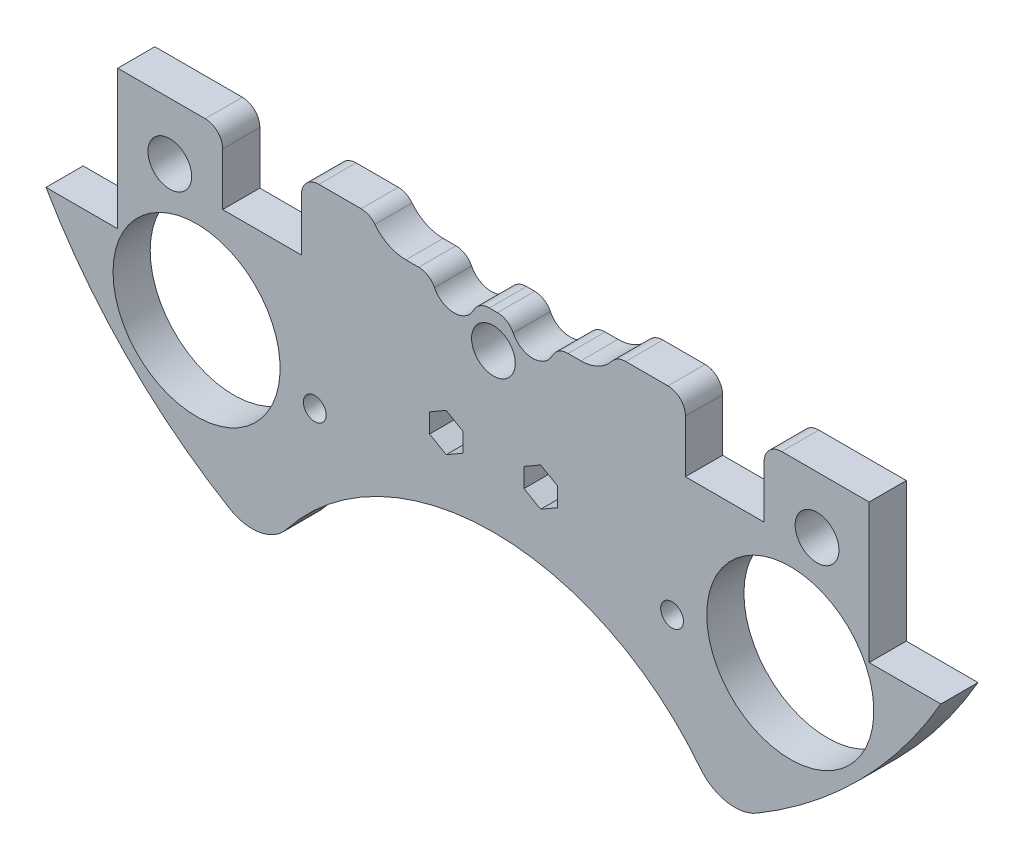
SolidWorks part; units mm, degrees
ref_plane "Front Plane" through (0, 0, 0) normal (0, 0, 1) x (1, 0, 0)
ref_plane "Top Plane" through (0, 0, 0) normal (0, 1, 0) x (1, 0, 0)
ref_plane "Right Plane" through (0, 0, 0) normal (1, 0, 0) x (0, 0, -1)
sketch "Sketch1" plane through (0, 0, 0) normal (0, 0, 1) x (1, 0, 0)
  line L0 (0, 0) -> (-82.1241, 0) construction
  line L1 (0, 0) -> (0, 95.6219) construction
  line L3 (-64.9644, 37.338) -> (-54.5504, 37.338)
  line L5 (-64.9644, -37.338) -> (-54.5504, -37.338)
  line L6 (-54.5504, 37.338) -> (-54.5504, -37.338)
  line L7 (64.9644, -37.338) -> (54.5504, -37.338)
  line L8 (64.9644, 37.338) -> (54.5504, 37.338)
  line L9 (54.5504, 37.338) -> (54.5504, -37.338)
  arc A0 (-64.9644, -37.338) -> (64.9644, -37.338) centre (0, 0) ccw
  circle A1 centre (-46.482, 11.049) radius 1.651
  circle A2 centre (-21.0833, 10.795) radius 1.651
  circle A3 centre (-21.0833, -10.795) radius 1.651
  circle A4 centre (-46.482, -11.049) radius 1.651
  circle A5 centre (46.482, -11.049) radius 1.651
  circle A6 centre (21.0833, -10.795) radius 1.651
  circle A7 centre (21.0833, 10.795) radius 1.651
  circle A8 centre (46.482, 11.049) radius 1.651
  arc A9 (64.9644, 37.338) -> (-64.9644, 37.338) centre (0, 0) ccw
  dimension "D2" = 3.302
  dimension "D3" = 3.302
  dimension "D4" = 25.4
  dimension "D5" = 10.795
  dimension "D10" = 46.482
  dimension "D6" = 74.676
  dimension "D7" = 10.414
  dimension "D8" = 74.93
  dimension "D9" = 74.93
  dimension "D11" = 37.338
extrude "Boss-Extrude2" add sketch "Sketch1" along normal blind 5.3975
sketch "Sketch2" plane through (0, 0, 5.3975) normal (0, 0, 1) x (1, 0, 0)
  line L0 (0, 68.58) -> (0, 55.88) construction
  line L1 (-9.525, 68.58) -> (9.525, 68.58)
  line L2 (-9.525, 68.58) -> (-9.525, 55.88)
  line L3 (-9.525, 55.88) -> (9.525, 55.88)
  line L4 (9.525, 68.58) -> (9.525, 55.88)
  line L5 (-9.525, 62.23) -> (9.525, 62.23) construction
  arc A0 (64.9644, 37.338) -> (-64.9644, 37.338) centre (0, 0) ccw construction
  circle A1 centre (-21.0833, 10.795) radius 1.651 construction
  circle A2 centre (21.0833, 10.795) radius 1.651 construction
  circle A3 centre (-6.731, 62.23) radius 1.143
  circle A4 centre (6.731, 62.23) radius 1.143
  dimension "D4" = 2.286
  dimension "D5" = 0
  dimension "D6" = 6.731
  dimension "D1" = 19.05
  dimension "D2" = 12.7
  dimension "D3" = 55.88
extrude "Cut-Extrude1" cut sketch "Sketch2" against normal through all contours A3 | A4
sketch "Sketch3" plane through (0, 0, 0) normal (0, 0, -1) x (-1, 0, 0)
  line L0 (0, 0) -> (0, -116.2908) construction
  line L1 (0, 0) -> (-153.8039, 0) construction
  line L2 (0, 0) -> (15.2681, -56.9814) construction
  circle A4 centre (-43.1052, -43.1052) radius 12.1285
  circle A6 centre (14.224, -34.29) radius 12.1285
  circle A7 centre (14.224, 34.29) radius 12.1285
  circle A8 centre (-43.1052, 43.1052) radius 12.1285
  circle A11 centre (43.1052, 43.1052) radius 12.1285
  circle A12 centre (-14.224, 34.29) radius 12.1285
  circle A13 centre (-14.224, -34.29) radius 12.1285
  circle A14 centre (43.1052, -43.1052) radius 12.1285
  point P36 (0, 0)
  point P53 (0, 0)
  point P55 (0, 0)
  dimension "D1" = 14.224
  dimension "D2" = 34.29
  dimension "D4" = 15
  dimension "D8" = 24.257
extrude "Cut-Extrude2" cut sketch "Sketch3" against normal through all
sketch "Sketch4" plane through (0, 0, 0) normal (0, 0, -1) x (-1, 0, 0)
  line L1 (-15.7702, 56.3138) -> (12.7925, 56.3138)
  line L2 (-15.7702, 56.3138) -> (-15.7702, 67.9913)
  line L3 (-15.7702, 67.9913) -> (12.7925, 67.9913)
  line L4 (12.7925, 56.3138) -> (12.7925, 67.9913)
extrude "Boss-Extrude3" add sketch "Sketch4" against normal up to surface (5.3975 mm away) up to face at (-55.2337, -43.1052, 5.3975)
sketch "Sketch5" plane through (0, 0, 0) normal (0, 0, -1) x (-1, 0, 0)
  line L1 (-85.044, -17.145) -> (131.6774, -17.145)
  line L2 (-85.044, -17.145) -> (-85.044, 113.4242)
  line L3 (-85.044, 113.4242) -> (131.6774, 113.4242)
  line L4 (131.6774, -17.145) -> (131.6774, 113.4242)
  circle A0 centre (-21.0833, -10.795) radius 1.651 construction
  dimension "D1" = 6.35
extrude "Cut-Extrude4" cut sketch "Sketch5" against normal through all contours L2 L3 L4 L1
sketch "Sketch6" plane through (0, 0, 0) normal (0, 0, -1) x (-1, 0, 0)
  line L0 (-33.02, -67.2621) -> (33.02, -67.2621)
  line L1 (0, 0) -> (0, -146.3858) construction
  arc A0 (-64.9644, -37.338) -> (64.9644, -37.338) centre (0, 0) ccw construction
  circle A1 centre (0, -86.3121) radius 38.1
  dimension "D2" = 76.2
  dimension "D1" = 66.04
  dimension "D3" = 19.05
extrude "Cut-Extrude5" cut sketch "Sketch6" against normal blind 60.96 contours A1
extrude "Cut-Extrude6" cut sketch "Sketch7" against normal through all both and the other way through all
sketch "Sketch7" plane through (-31.3134, 132.614, 31.75) normal (0, 0, 1) x (0, 1, 0)
  line L0 (-132.614, -31.3134) -> (-132.614, 57.8454) construction
  line L1 (-132.614, -31.3134) -> (-222.516, -31.3134) construction
  circle A0 centre (-158.014, 14.4066) radius 3.175
  circle A1 centre (-173.254, -31.3134) radius 3.175
  circle A3 centre (-158.014, -77.0334) radius 3.175
  circle A4 centre (-107.214, -77.0334) radius 3.175
  circle A5 centre (-91.974, -31.3134) radius 3.175
  circle A6 centre (-107.214, 14.4066) radius 3.175
fillet "Fillet1" radius 6.35 1 edges at (-33.001, -67.2714, 2.6987)
fillet "Fillet2" radius 6.35 1 edges at (33.001, -67.2714, 2.6987)
extrude "Cut-Extrude8" cut sketch "Sketch9" against normal blind 29.21
sketch "Sketch9" plane through (-31.3134, 132.559, 28.575) normal (0, 0, 1) x (0, 1, 0)
  line L0 (-132.559, -31.3134) -> (6.1626, -31.3134) construction
  line L2 (-132.559, -31.3134) -> (-132.559, -122.6589) construction
  circle A0 centre (-190.979, 2.9766) radius 1.651
  circle A2 centre (-154.784, -31.3134) radius 1.651
  circle A3 centre (-190.979, -65.6034) radius 1.651
  circle A4 centre (-110.334, -31.3134) radius 1.651
  circle A5 centre (-74.139, -65.6034) radius 1.651
  circle A6 centre (-74.139, 2.9766) radius 1.651
extrude "Cut-Extrude99" cut sketch "Sketch100" against normal blind 29.21
sketch "Sketch100" plane through (-31.3134, 132.559, 22.225) normal (0, 0, 1) x (0, 1, 0)
  line L0 (-143.7712, -34.3645) -> (6.1626, -34.3645) construction
  line L2 (-143.7712, -34.3645) -> (-143.7712, -122.6589) construction
  circle A0 centre (-202.1912, -0.0745) radius 1.651
  circle A2 centre (-165.9962, -34.3645) radius 1.651
  circle A3 centre (-202.1912, -68.6545) radius 1.651
  circle A4 centre (-121.5462, -34.3645) radius 1.651
  circle A5 centre (-85.3512, -68.6545) radius 1.651
  circle A6 centre (-85.3512, -0.0745) radius 1.651
sketch "Sketch102" plane through (0, 0, 0) normal (0, 0, -1) x (-1, 0, 0)
  line L0 (-54.5504, -17.145) -> (54.5504, -17.145) construction
  line L1 (-39.3104, -17.145) -> (-27.8804, -17.145)
  line L2 (-39.3104, -17.145) -> (-39.3104, -27.305)
  line L3 (-39.3104, -27.305) -> (-27.8804, -27.305)
  line L4 (-27.8804, -17.145) -> (-27.8804, -27.305)
  line L5 (0, 15.7454) -> (0, -80.7771) construction
  line L6 (27.8804, -17.145) -> (39.3104, -17.145)
  line L7 (27.8804, -17.145) -> (27.8804, -27.305)
  line L8 (27.8804, -27.305) -> (39.3104, -27.305)
  line L9 (39.3104, -17.145) -> (39.3104, -27.305)
  line L10 (-54.5504, -37.338) -> (-54.5504, -17.145) construction
  dimension "D1" = 11.43
  dimension "D2" = 10.16
  dimension "D3" = 15.24
extrude "Cut-Extrude101" cut sketch "Sketch102" against normal through all
extrude "Cut-Extrude157" cut sketch "Sketch158" against normal blind 97.79
sketch "Sketch158" plane through (30.092, 4.0835, -24.638) normal (0, 0, -1) x (-1, 0, 0)
  line L0 (30.092, -29.4835) -> (30.092, 6.2385) construction
  circle A0 centre (4.1544, -49.7288) radius 1.651
  circle A4 centre (56.0296, -49.7288) radius 1.651
  circle A5 centre (4.1544, 41.3825) radius 1.651
  circle A9 centre (56.0296, 41.3825) radius 1.651
extrude "Cut-Extrude211" cut sketch "Sketch212" against normal blind 48.768 and the other way blind 103.378
sketch "Sketch212" plane through (30.092, 4.0835, 11.4935) normal (0, 0, -1) x (-1, 0, 0)
  line L0 (30.092, -4.0835) -> (148.6336, -4.0835) construction
  line L1 (30.092, -4.0835) -> (30.092, 90.452) construction
  circle A0 centre (-16.898, 21.3165) radius 3.175
  circle A1 centre (77.082, 21.3165) radius 3.175
  circle A2 centre (30.092, 21.3165) radius 3.175
  circle A4 centre (77.082, -29.4835) radius 3.175
  circle A5 centre (30.092, -29.4835) radius 3.175
  circle A6 centre (-16.898, -29.4835) radius 3.175
sketch "Sketch105" plane through (0, 0, 0) normal (0, 0, -1) x (-1, 0, 0)
  line L0 (0, 0) -> (0, -8.89) construction
  line L1 (-12.7, -20.32) -> (-8.89, -20.32)
  line L2 (-12.7, -8.89) -> (12.7, -8.89)
  line L3 (0, -20.32) -> (0, -99.3188) construction
  line L4 (8.89, -20.32) -> (12.7, -20.32)
  line L5 (-2.54, -20.32) -> (2.54, -20.32)
  arc A0 (-12.7, -8.89) -> (-12.7, -20.32) centre (-12.7, -14.605) ccw
  arc A1 (12.7, -8.89) -> (12.7, -20.32) centre (12.7, -14.605) cw
  arc A2 (-8.89, -20.32) -> (-2.54, -20.32) centre (-5.715, -20.32) ccw
  arc A3 (2.54, -20.32) -> (8.89, -20.32) centre (5.715, -20.32) ccw
  dimension "D1" = 11.43
  dimension "D4" = 6.35
  dimension "D5" = 6.35
  dimension "D2" = 12.7
  dimension "D3" = 14.605
  dimension "D6" = 11.43
  dimension "D7" = 5.715
  dimension "D8" = 20.32
extrude "Cut-Extrude104" cut sketch "Sketch105" against normal blind 10
fillet "Fillet3" radius 2.54 10 edges at (-39.3104, -17.145, 2.6987) (-27.8804, -17.145, 2.6987) (-17.8195, -17.145, 2.6987) (-8.89, -20.32, 2.6987) (-2.54, -20.32, 2.6987) (2.54, -20.32, 2.6987) (8.89, -20.32, 2.6987) (17.8195, -17.145, 2.6987) (27.8804, -17.145, 2.6987) (39.3104, -17.145, 2.6987)
sketch "Sketch225" plane through (0, 0, 0) normal (0, 0, -1) x (-1, 0, 0)
  circle A0 centre (-14.224, -34.29) radius 12.1285
  circle A1 centre (14.224, -34.29) radius 12.1285
  circle A2 centre (-14.224, -34.29) radius 12.1285 construction
  circle A3 centre (14.224, -34.29) radius 12.1285 construction
extrude "Boss-Extrude4" add sketch "Sketch225" against normal up to surface (5.3975 mm away) up to face at (0, -26.8535, 5.3975)
sketch "Sketch226" plane through (0, 0, 0) normal (0, 0, -1) x (-1, 0, 0)
  line L1 (4.445, -37.7229) -> (4.445, -40.5091)
  line L2 (4.445, -40.5091) -> (6.858, -41.9023)
  line L3 (6.858, -41.9023) -> (9.271, -40.5091)
  line L4 (9.271, -40.5091) -> (9.271, -37.7229)
  line L5 (9.271, -37.7229) -> (6.858, -36.3297)
  line L6 (6.858, -36.3297) -> (4.445, -37.7229)
  line L7 (-4.445, -37.7229) -> (-6.858, -36.3297)
  line L8 (-6.858, -36.3297) -> (-9.271, -37.7229)
  line L9 (-9.271, -37.7229) -> (-9.271, -40.5091)
  line L10 (-9.271, -40.5091) -> (-6.858, -41.9023)
  line L11 (-6.858, -41.9023) -> (-4.445, -40.5091)
  line L12 (-4.445, -40.5091) -> (-4.445, -37.7229)
  circle A0 centre (6.858, -39.116) radius 2.413 construction
  circle A1 centre (-6.858, -39.116) radius 2.413 construction
  arc A2 (-64.9644, -37.338) -> (-38.2787, -64.4146) centre (0, 0) ccw construction
  dimension "D1" = 4.826
  dimension "D2" = 4.826
  dimension "D3" = 13.716
  dimension "D4" = 6.858
  dimension "D5" = 39.116
  dimension "D6" = 0
extrude "Cut-Extrude224" cut sketch "Sketch226" against normal through all
